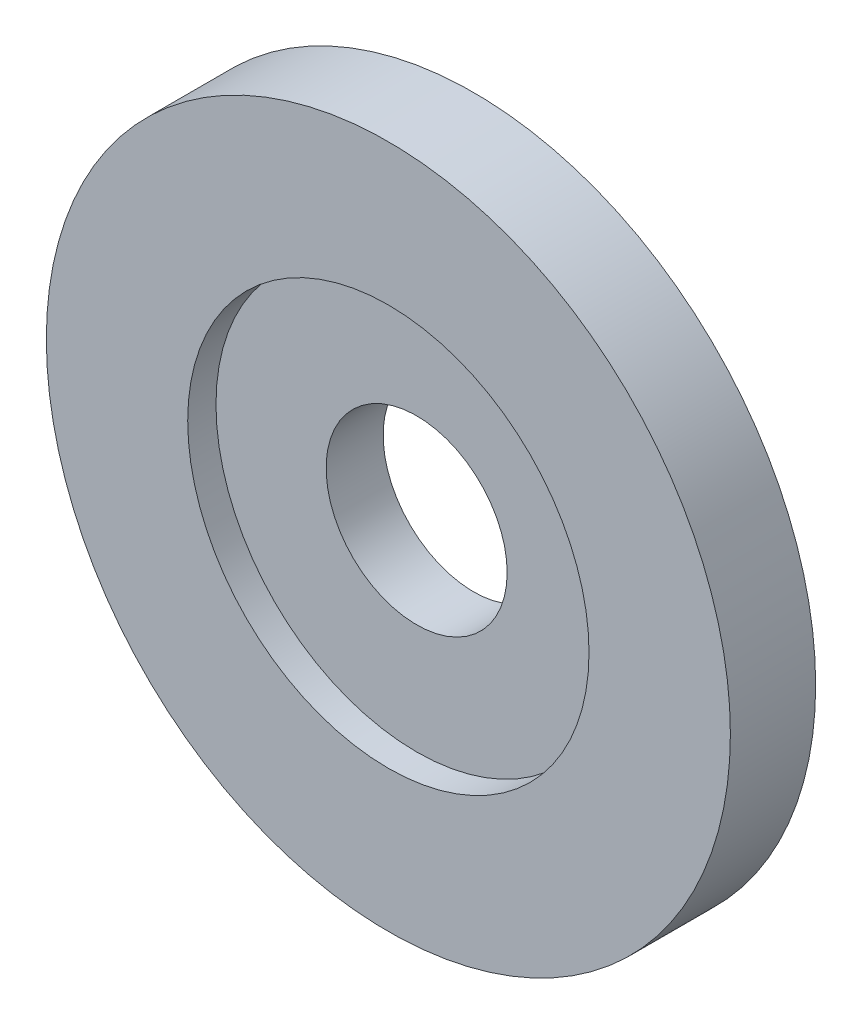
SolidWorks part; units mm, degrees
material "ABS"
ref_plane "Front Plane" through (0, 0, 0) normal (0, 0, 1) x (1, 0, 0)
ref_plane "Top Plane" through (0, 0, 0) normal (0, 1, 0) x (1, 0, 0)
ref_plane "Right Plane" through (0, 0, 0) normal (1, 0, 0) x (0, 0, -1)
sketch "Sketch1" plane through (0, 0, 0) normal (0, 0, 1) x (1, 0, 0)
  circle A0 centre (-35.2684, -193.372) radius 19.05
  circle A1 centre (-35.2684, -193.372) radius 5.0419
  dimension "D1" = 38.1
  dimension "D2" = 10.0838
extrude "Boss-Extrude1" add sketch "Sketch1" along normal blind 3.175
sketch "Sketch2" plane through (0, 0, 3.175) normal (0, 0, 1) x (1, 0, 0)
  circle A0 centre (-35.2684, -193.372) radius 19.05
  circle A1 centre (-35.2684, -193.372) radius 11.176
  dimension "D1" = 38.1
  dimension "D2" = 22.352
extrude "Boss-Extrude2" add sketch "Sketch2" along normal blind 1.5748
